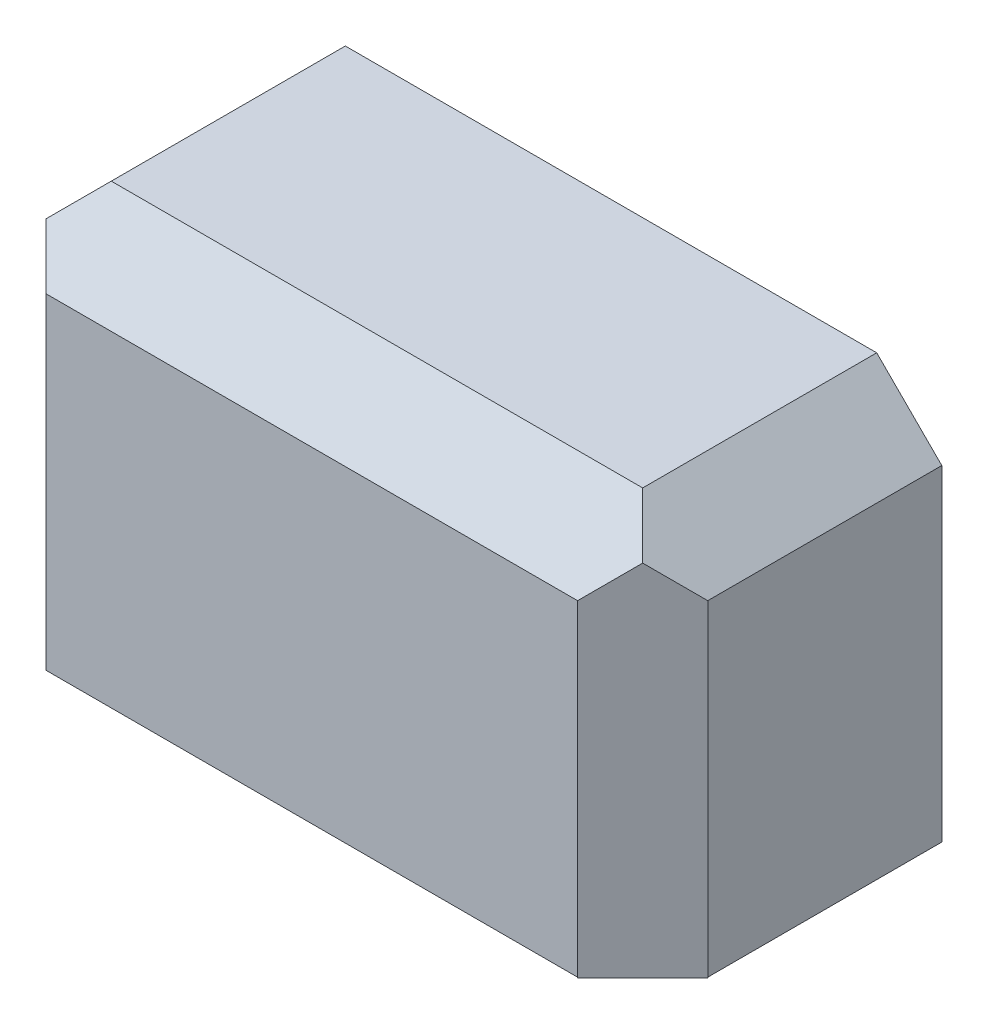
SolidWorks part; units mm, degrees
ref_plane "Front Plane" through (0, 0, 0) normal (0, 0, 1) x (1, 0, 0)
ref_plane "Top Plane" through (0, 0, 0) normal (0, 1, 0) x (1, 0, 0)
ref_plane "Right Plane" through (0, 0, 0) normal (1, 0, 0) x (0, 0, -1)
sketch "Sketch13" plane through (0, 0, 0) normal (0, 0, 1) x (1, 0, 0)
  line L0 (0, 0) -> (0, 179.979)
  line L1 (0, 179.979) -> (35.921, 215.9)
  line L2 (35.921, 215.9) -> (329.204, 215.9)
  line L3 (329.204, 215.9) -> (365.125, 179.979)
  line L4 (365.125, 179.979) -> (365.125, 0)
  line L5 (365.125, 0) -> (0, 0)
  dimension "D1" = 50.8
  dimension "D2" = 50.8
  dimension "D3" = 215.9
  dimension "D4" = 135
  dimension "D5" = 365.125
extrude "Boss-Extrude3" add sketch "Sketch13" along normal blind 165.1
sketch "Sketch14" plane through (0, 0, 165.1) normal (0, 0, 1) x (1, 0, 0)
  line L0 (4.7625, 0) -> (4.7625, 177.7948)
  line L1 (0, 0) -> (365.125, 0) construction
  line L2 (4.7625, 177.7948) -> (38.1052, 211.1375)
  line L3 (38.1052, 211.1375) -> (327.2313, 211.1375)
  line L4 (327.2313, 211.1375) -> (360.3625, 178.0063)
  line L5 (360.3625, 178.0063) -> (360.3625, 0)
  line L6 (0, 179.979) -> (0, 0) construction
  line L7 (35.921, 215.9) -> (0, 179.979) construction
  line L8 (329.204, 215.9) -> (35.921, 215.9) construction
  line L9 (365.125, 179.979) -> (329.204, 215.9) construction
  line L10 (365.125, 0) -> (365.125, 179.979) construction
  line L11 (4.7625, 0) -> (360.3625, 0)
  dimension "D1" = 4.7625
  dimension "D2" = 4.9121
  dimension "D3" = 4.7625
  dimension "D4" = 4.7625
  dimension "D5" = 4.7625
extrude "Cut-Extrude1" cut sketch "Sketch14" against normal blind 160.3375
sketch "Sketch15" plane through (0, 0, 165.1) normal (0, 0, 1) x (1, 0, 0)
  line L0 (0, 0) -> (0, 179.979)
  line L1 (0, 179.979) -> (35.921, 215.9)
  line L2 (35.921, 215.9) -> (329.204, 215.9)
  line L3 (329.204, 215.9) -> (365.125, 179.979)
  line L4 (365.125, 179.979) -> (365.125, 0)
  line L5 (365.125, 0) -> (0, 0)
extrude "Boss-Extrude4" add sketch "Sketch15" against normal blind 4.7625
sketch "Sketch16" plane through (365.125, 0, 0) normal (1, 0, 0) x (0, 0, -1)
  line L0 (-165.1, 179.979) -> (-129.179, 215.9)
  line L1 (-165.1, 215.9) -> (0, 215.9) construction
  line L2 (-129.179, 215.9) -> (-165.1, 215.9)
  line L3 (-165.1, 215.9) -> (-165.1, 179.979)
extrude "Cut-Extrude2" cut sketch "Sketch16" against normal blind 387.2865 and the other way blind 11.176
sketch "Sketch17" plane through (365.125, 0, 0) normal (1, 0, 0) x (0, 0, -1)
  line L0 (-165.1, 179.979) -> (-129.179, 215.9)
  line L1 (-129.179, 215.9) -> (-125.8114, 212.5324)
  line L2 (-125.8114, 212.5324) -> (-161.7324, 176.6114)
  line L3 (-161.7324, 176.6114) -> (-165.1, 179.979)
  dimension "D1" = 4.7625
extrude "Boss-Extrude5" add sketch "Sketch17" against normal blind 365.125
sketch "Sketch18" plane through (0, 0, 0) normal (0, 0, -1) x (-1, 0, 0)
  line L0 (-365.125, 179.979) -> (-329.204, 215.9)
  line L1 (-329.204, 215.9) -> (-365.125, 215.9)
  line L2 (-365.125, 215.9) -> (-365.125, 179.979)
  line L3 (-35.921, 215.9) -> (0, 215.9)
  line L4 (0, 215.9) -> (0, 179.979)
  line L5 (0, 179.979) -> (-35.921, 215.9)
extrude "Cut-Extrude3" cut sketch "Sketch18" against normal blind 365.125
sketch "Sketch19" plane through (0, 215.9, 0) normal (0, 1, 0) x (1, 0, 0)
  line L0 (35.921, -129.179) -> (0, -129.179) construction
  line L1 (0, -165.1) -> (0, 0) construction
  line L2 (0, -129.179) -> (0, -165.1) construction
  line L3 (0, -165.1) -> (35.921, -165.1) construction
  line L4 (365.125, -165.1) -> (0, -165.1) construction
  line L5 (35.921, -165.1) -> (35.921, -129.179) construction
  line L6 (0, -129.179) -> (35.921, -165.1)
  line L7 (0, -129.179) -> (0, -165.1)
  line L8 (0, -165.1) -> (35.921, -165.1)
extrude "Cut-Extrude4" cut sketch "Sketch19" against normal blind 365.125
sketch "Sketch20" plane through (0, 215.9, 0) normal (0, 1, 0) x (1, 0, 0)
  line L0 (0, -129.179) -> (35.921, -165.1)
  line L1 (0, -129.179) -> (3.3676, -125.8114)
  line L2 (35.921, -165.1) -> (39.2886, -161.7324)
  line L3 (3.3676, -125.8114) -> (39.2886, -161.7324)
  dimension "D1" = 4.7625
extrude "Boss-Extrude6" add sketch "Sketch20" against normal blind 216.027 and the other way blind 1.27
sketch "Sketch21" plane through (365.125, 0, 0) normal (1, 0, 0) x (0, 0, -1)
  line L0 (-165.1, 179.979) -> (-129.179, 215.9)
  line L1 (-129.179, 215.9) -> (-125.0603, 215.9)
  line L2 (-129.179, 215.9) -> (0, 215.9) construction
  line L3 (-125.0603, 215.9) -> (-125.0603, 220.6015)
  line L4 (-125.0603, 220.6015) -> (-193.2403, 220.6015)
  line L5 (-193.2403, 220.6015) -> (-185.7192, 179.979)
  line L6 (-185.7192, 179.979) -> (-165.1, 179.979)
extrude "Cut-Extrude5" cut sketch "Sketch21" against normal blind 398.907
sketch "Sketch22" plane through (0, 0, 0) normal (0, 0, -1) x (-1, 0, 0)
  line L0 (0, 179.979) -> (-35.921, 215.9)
  line L1 (0, 179.979) -> (20.3751, 200.354)
  line L2 (-35.921, 215.9) -> (-15.546, 236.2751)
  line L3 (20.3751, 200.354) -> (-15.546, 236.2751)
extrude "Cut-Extrude7" cut sketch "Sketch22" against normal blind 398.907
sketch "Sketch24" plane through (0, 215.9, 0) normal (0, 1, 0) x (1, 0, 0)
  line L0 (329.204, -129.179) -> (365.125, -129.179) construction
  line L1 (365.125, -165.1) -> (365.125, 0) construction
  line L2 (365.125, -129.179) -> (329.204, -129.179) construction
  line L3 (329.204, -129.179) -> (329.204, -165.1) construction
  line L4 (365.125, -165.1) -> (35.921, -165.1) construction
  line L5 (329.204, -165.1) -> (365.125, -129.179)
  line L6 (329.204, -165.1) -> (351.4839, -187.3799)
  line L7 (365.125, -129.179) -> (387.4049, -151.4589)
  line L8 (351.4839, -187.3799) -> (387.4049, -151.4589)
extrude "Cut-Extrude8" cut sketch "Sketch24" against normal blind 216.281
sketch "Sketch25" plane through (0, 215.9, 0) normal (0, 1, 0) x (1, 0, 0)
  line L0 (329.204, -165.1) -> (365.125, -129.179)
  line L1 (329.204, -165.1) -> (325.8364, -161.7324)
  line L2 (365.125, -129.179) -> (361.7574, -125.8114)
  line L3 (325.8364, -161.7324) -> (361.7574, -125.8114)
  dimension "D1" = 4.7625
extrude "Boss-Extrude7" add sketch "Sketch25" against normal blind 216.281
sketch "Sketch26" plane through (0, 0, 0) normal (0, 0, -1) x (-1, 0, 0)
  line L0 (-365.125, 179.979) -> (-329.204, 215.9)
  line L1 (-365.125, 179.979) -> (-393.0791, 207.9331)
  line L2 (-329.204, 215.9) -> (-357.1581, 243.8541)
  line L3 (-393.0791, 207.9331) -> (-357.1581, 243.8541)
extrude "Cut-Extrude9" cut sketch "Sketch26" against normal blind 216.281
sketch "Sketch27" plane through (0, 0, 0) normal (-1, 0, 0) x (0, 0, 1)
  line L0 (129.179, 215.9) -> (165.1, 179.979)
  line L1 (129.179, 215.9) -> (149.6396, 236.3607)
  line L2 (165.1, 179.979) -> (185.5607, 200.4396)
  line L3 (149.6396, 236.3607) -> (185.5607, 200.4396)
extrude "Cut-Extrude10" cut sketch "Sketch27" against normal blind 2540
